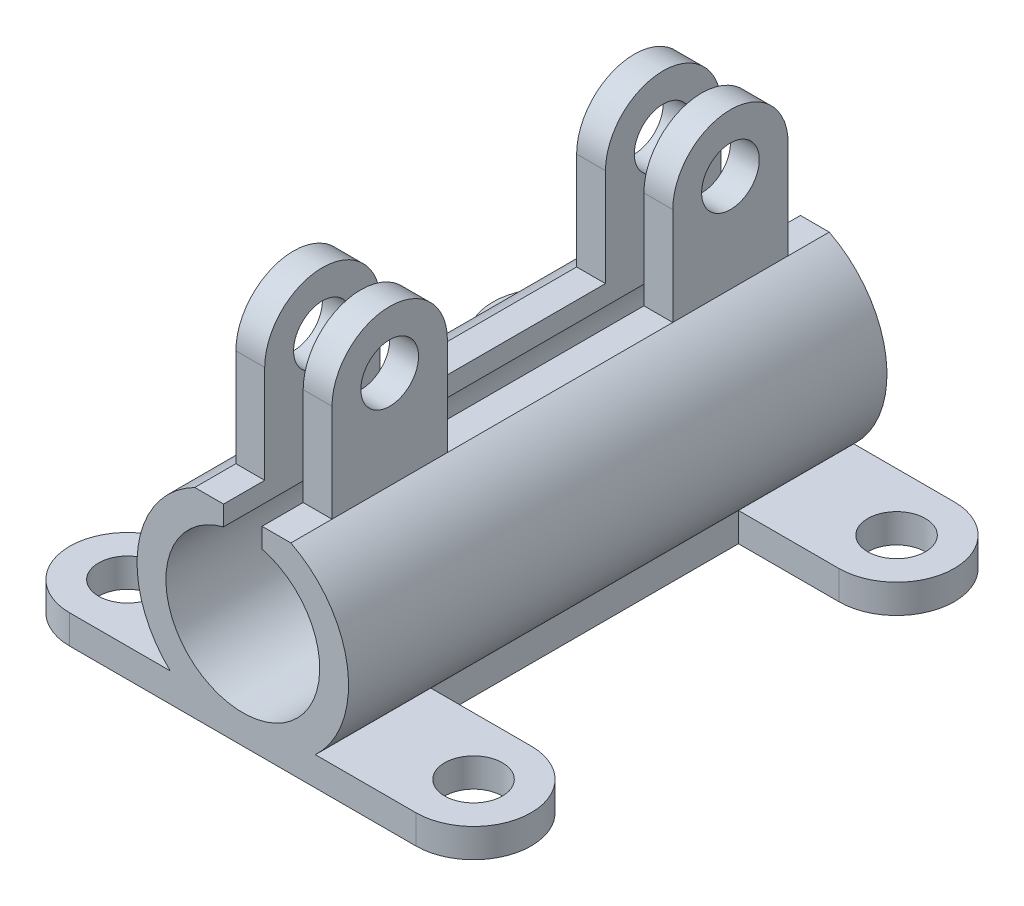
SolidWorks part; units mm, degrees
ref_plane "Front Plane" through (0, 0, 0) normal (0, 0, 1) x (1, 0, 0)
ref_plane "Top Plane" through (0, 0, 0) normal (0, 1, 0) x (1, 0, 0)
ref_plane "Right Plane" through (0, 0, 0) normal (1, 0, 0) x (0, 0, -1)
sketch "Sketch1" plane through (0, 0, 0) normal (0, 0, 1) x (1, 0, 0)
  line L0 (-120, 0) -> (120, 0)
  line L1 (-120, 15) -> (-37.7492, 15)
  line L2 (-120, 15) -> (-120, 0)
  line L3 (120, 15) -> (120, 0)
  line L4 (37.7492, 15) -> (120, 15)
  line L5 (-120, 15) -> (120, 15) construction
  line L6 (0, -66.1007) -> (0, 15) construction
  line L7 (-25, 103.9898) -> (-10, 103.9898)
  line L8 (25, 103.9898) -> (10, 103.9898)
  line L13 (-10, 93.7298) -> (-10, 103.9898)
  line L15 (10, 93.7298) -> (10, 103.9898)
  arc A0 (37.7492, 15) -> (25, 103.9898) centre (0, 55) ccw
  arc A1 (-10, 93.7298) -> (10, 93.7298) centre (0, 55) ccw
  arc A2 (-25, 103.9898) -> (-37.7492, 15) centre (0, 55) ccw
  point P4 (0, 0)
  dimension "D3" = 110
  dimension "D4" = 80
  dimension "D1" = 240
  dimension "D5" = 55
  dimension "D9" = 10
  dimension "D2" = 15
extrude "Boss-Extrude1" add sketch "Sketch1" along normal blind 280
ref_plane "Plane2" through (-10, 0, 0) normal (1, 0, 0) x (0, 0, -1)
sketch "Sketch4" plane through (-10, 0, 0) normal (1, 0, 0) x (0, 0, -1)
  line L0 (-258.6049, 154.8327) -> (-258.6049, 103.9898)
  line L1 (-280, 103.9898) -> (0, 103.9898) construction
  line L2 (-198.6049, 154.8327) -> (-198.6049, 103.9898)
  line L3 (-198.6049, 103.9898) -> (-258.6049, 103.9898)
  line L4 (-140, 207.0164) -> (-140, -32.0418) construction
  line L5 (-81.3951, 103.9898) -> (-21.3951, 103.9898)
  line L6 (-21.3951, 154.8327) -> (-21.3951, 103.9898)
  line L7 (-81.3951, 154.8327) -> (-81.3951, 103.9898)
  circle A0 centre (-228.6049, 154.8327) radius 15
  arc A1 (-198.6049, 154.8327) -> (-258.6049, 154.8327) centre (-228.6049, 154.8327) ccw
  circle A2 centre (-51.3951, 154.8327) radius 15
  arc A3 (-81.3951, 154.8327) -> (-21.3951, 154.8327) centre (-51.3951, 154.8327) cw
  dimension "D1" = 30
  dimension "D2" = 60
extrude "Boss-Extrude2" add sketch "Sketch4" against normal blind 15
mirror "Mirror1" about plane through (0, 0, 0) normal (1, 0, 0) of "Boss-Extrude2"
sketch "Sketch5" plane through (0, 15, 0) normal (0, 1, 0) x (1, 0, 0)
  line L0 (90, 0) -> (120, 0)
  line L1 (37.7492, -60) -> (37.7492, -220)
  line L2 (90, -280) -> (120, -280)
  line L3 (120, -280) -> (120, 0)
  line L4 (90, -60) -> (37.7492, -60)
  line L5 (90, -220) -> (37.7492, -220)
  arc A0 (90, -60) -> (90, 0) centre (90, -30) ccw
  arc A1 (90, -280) -> (90, -220) centre (90, -250) ccw
  line M4 (120, 0) -> (37.7492, 0)
  line M5 (37.7492, 0) -> (37.7492, -280)
  line M6 (37.7492, -280) -> (120, -280)
  line M7 (120, -280) -> (120, 0)
  dimension "D1" = 60
  dimension "D2" = 30
extrude "Cut-Extrude1" cut sketch "Sketch5" against normal blind 15 contours A1 L3 A0 L4 L5 M5 | A0 L3 M4 | A1 M6 M7
sketch "Sketch7" plane through (0, 15, 0) normal (0, 1, 0) x (1, 0, 0)
  line L0 (-37.7492, 0) -> (-37.7492, -280)
  line L1 (-90, 0) -> (-37.7492, 0)
  line L2 (-120, -280) -> (-120, 0)
  line L3 (-90, -280) -> (-37.7492, -280)
  line L4 (-90, -60) -> (-37.7492, -60)
  line L5 (-90, -220) -> (-37.7492, -220)
  line L6 (-90, -280) -> (-120, -280)
  arc A0 (-90, 0) -> (-90, -60) centre (-90, -30) ccw
  arc A1 (-90, -220) -> (-90, -280) centre (-90, -250) ccw
  line M3 (-37.7492, 0) -> (-120, 0)
  line M4 (-120, 0) -> (-120, -280)
  line M5 (-120, -280) -> (-37.7492, -280)
  dimension "D5" = 60
  dimension "D6" = 60
  dimension "D2" = 30
  dimension "D4" = 30
extrude "Cut-Extrude2" cut sketch "Sketch7" against normal blind 15 contours A1 L5 L0 L4 A0 L2 | A0 M3 M4 | A1 M4 M5
sketch "Sketch9" plane through (0, 15, 0) normal (0, 1, 0) x (1, 0, 0)
  circle A0 centre (90, -30) radius 15
  dimension "D1" = 30
extrude "Cut-Extrude3" cut sketch "Sketch9" against normal blind 15
pattern_linear "LPattern1" count 2 spacing 180 along (-1, 0, 0) of "Cut-Extrude3"
pattern_linear "LPattern2" count 2 spacing 220 along (0, 0, 1) of "Cut-Extrude3", "LPattern1"
